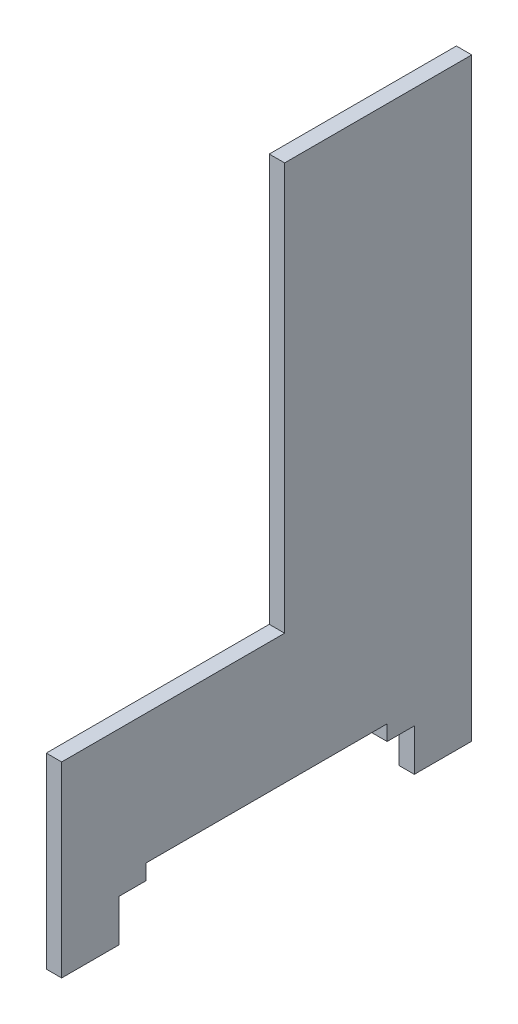
SolidWorks part; units mm, degrees
ref_plane "Front Plane" through (0, 0, 0) normal (0, 0, 1) x (1, 0, 0)
ref_plane "Top Plane" through (0, 0, 0) normal (0, 1, 0) x (1, 0, 0)
ref_plane "Right Plane" through (0, 0, 0) normal (1, 0, 0) x (0, 0, -1)
sketch "Sketch1" plane through (0, 0, 0) normal (0, 1, 0) x (1, 0, 0)
  line L0 (0, 0) -> (0, 40) construction
  line L1 (-40, 40) -> (40, 40) construction
  line L2 (-40, 40) -> (-40, -40) construction
  line L3 (-40, -40) -> (40, -40) construction
  line L4 (40, 40) -> (40, -40) construction
  line L5 (0, 0) -> (-40, 0) construction
  line L6 (-20, 60) -> (60, 60) construction
  line L7 (-37, -37) -> (37, -37) construction
  line L8 (37, 37) -> (37, -37) construction
  line L9 (-37, 37) -> (37, 37) construction
  line L10 (-37, 37) -> (-37, -37) construction
  line L11 (-37, -37) -> (-40, -37) construction
  line L12 (14.7, 20) -> (17.7, 20) construction
  line L13 (40, -31.8) -> (-40, -31.8) construction
  line L14 (-40, -28.8) -> (40, -28.8) construction
  line L15 (-40, -23.5) -> (40, -23.5) construction
  line L16 (0, -31.8) -> (0, -28.8) construction
  line L17 (0, -31.8) -> (0, -40) construction
  line L18 (0, -28.8) -> (0, -23.5) construction
  line L19 (43.5, 20) -> (48.8, 20) construction
  line L20 (51.8, 20) -> (60, 20) construction
  line L21 (40, 2.3) -> (-40, 2.3) construction
  line L22 (-40, 5.3) -> (40, 5.3) construction
  line L23 (3, 5.3) -> (3, 2.3) construction
  line L25 (40, -0.7) -> (-40, -0.7) construction
  line L26 (40, 8.3) -> (-40, 8.3) construction
  line L27 (3, 2.3) -> (3, -0.7) construction
  line L28 (3, 5.3) -> (3, 8.3) construction
  line L29 (17.7, 20) -> (20.7, 20) construction
  line L30 (19, 20) -> (56.5, 20) construction
  line L31 (3, 0) -> (0, 0) construction
  line L33 (40, 31.8) -> (-40, 31.8) construction
  line L34 (-40, 28.8) -> (40, 28.8) construction
  line L35 (-40, 23.5) -> (40, 23.5) construction
  line L36 (6, 2.3) -> (6, 1) construction
  line L37 (6, -36.5) -> (6, -40) construction
  line L38 (56.5, 20) -> (60, 20) construction
  line L40 (3, 0) -> (6, 0) construction
  line L41 (6, 1) -> (6, -36.5) construction
  line L42 (19, 20) -> (17.7, 20) construction
sketch "Sketch2" plane through (0, 0, 0) normal (1, 0, 0) x (0, 0, -1)
  line L0 (40, 0) -> (-40, 0) construction
  line L1 (40, 3.55) -> (-40, 3.55)
  line L2 (40, 3.55) -> (40, 119.507)
  line L3 (40, 119.507) -> (-40, 119.507) construction
  line L4 (-40, 3.55) -> (-40, 119.507) construction
  line L5 (40, -3.55) -> (-40, -3.55) construction
  line L6 (0, 0) -> (0, 119.507) construction
  line L7 (20, -5.5) -> (20, -47.5) construction
  line L8 (5.3, 47.5) -> (2.3, 47.5)
  line L9 (5.3, 47.5) -> (5.3, 5.5)
  line L10 (5.3, 5.5) -> (2.3, 5.5)
  line L11 (2.3, 47.5) -> (2.3, 5.5)
  line L12 (5.3, 5.5) -> (5.3, 3.55) construction
  line L13 (20, -5.5) -> (20, -3.55) construction
  line L14 (5.3, 26.5) -> (-36.5, 26.5) construction
  line L15 (20, -16.45) -> (20, -36.55) construction
  line L16 (-36.5, 36.55) -> (1, 36.55)
  line L17 (-36.5, 36.55) -> (-36.5, 16.45)
  line L18 (-36.5, 16.45) -> (1, 16.45)
  line L19 (1, 36.55) -> (1, 16.45)
  line L20 (37, 116.507) -> (37, 6.55) construction
  line L21 (37, 6.55) -> (-37, 6.55) construction
  line L22 (-37, 6.55) -> (-37, 116.507) construction
  line L23 (-37, 6.55) -> (-37, 3.55) construction
  line L24 (-37, 6.55) -> (-40, 6.55) construction
  line L25 (-23.5, 3.55) -> (-23.5, 6.55)
  line L26 (-23.5, 6.55) -> (-28.8, 6.55)
  line L27 (-28.8, 6.55) -> (-28.8, 11.75)
  line L28 (-28.8, 11.75) -> (-23.5, 11.75)
  line L29 (-23.5, 11.75) -> (-23.5, 14.75)
  line L30 (-23.5, 14.75) -> (-40, 14.75)
  line L31 (-31.8, 14.75) -> (-31.8, 3.55) construction
  line L32 (20, -6.55) -> (20, -11.75) construction
  line L33 (31.8, 14.75) -> (31.8, 3.55) construction
  line L34 (23.5, 14.75) -> (40, 14.75)
  line L35 (23.5, 11.75) -> (23.5, 14.75)
  line L36 (28.8, 11.75) -> (23.5, 11.75)
  line L37 (28.8, 6.55) -> (28.8, 11.75)
  line L38 (23.5, 6.55) -> (28.8, 6.55)
  line L39 (23.5, 3.55) -> (23.5, 6.55)
  line L40 (23.5, 14.75) -> (-23.5, 14.75) construction
  line L41 (37, 116.507) -> (-37, 116.507) construction
  line L43 (3.5, 119.507) -> (3.5, 40.05) construction
  line L44 (-37, 116.507) -> (-37, 119.507) construction
  line L45 (-37, 116.507) -> (-40, 116.507) construction
  line L46 (3.5, 40.05) -> (-40, 40.05)
  line L47 (6.5, 119.507) -> (6.5, 37.05) construction
  line L48 (6.5, 37.05) -> (-40, 37.05) construction
  line L49 (3.5, 40.05) -> (3.5, 37.05) construction
  line L50 (3.5, 40.05) -> (6.5, 40.05) construction
  line L51 (27.1, 60.207) -> (7, 60.207) construction
  line L52 (6.5, 37.05) -> (6.5, 3.55) construction
  line L53 (-36.5, 36.55) -> (-37, 36.55) construction
  line L54 (-36.5, 36.55) -> (-36.5, 37.05) construction
  line L55 (3.5, 37.05) -> (3.5, 3.55) construction
  line L56 (27.1, 60.207) -> (7, 60.207) construction
  line L57 (27.1, 60.207) -> (27.1, 114.507) construction
  line L58 (27.1, 114.507) -> (7, 114.507) construction
  line L59 (7, 60.207) -> (7, 114.507) construction
  line L60 (27.1, 114.507) -> (7, 114.507) construction
  line L61 (27.1, 107.857) -> (27.1, 66.857) construction
  line L62 (7, 107.857) -> (7, 66.857) construction
  line L63 (3.5, 98.4639) -> (6.5, 98.4639) construction
  line L64 (3.5, 55.3502) -> (6.5, 55.3502) construction
  circle A0 centre (17.05, 76.907) radius 21 construction
  circle A1 centre (17.05, 76.907) radius 21 construction
  circle A2 centre (17.05, 76.907) radius 24 construction
  dimension "D2" = 3
  dimension "D1" = 0.5
  dimension "D3" = 2
  dimension "D4" = 43.5
ref_plane "xslide" through (0, 26.5, 0) normal (0, 1, 0) x (1, 0, 0)
ref_plane "xgear" through (0, 0, -2.3) normal (0, 0, 1) x (1, 0, 0)
sketch "Sketch3" plane through (0, 0, 0) normal (0, 1, 0) x (1, 0, 0)
  line L0 (28.8, 31.8) -> (23.5, 31.8)
  line L1 (40, 40) -> (-40, 40)
  line L2 (40, 40) -> (40, -40)
  line L3 (40, -40) -> (-40, -40)
  line L4 (-40, 40) -> (-40, -40)
  line L5 (37, 37) -> (-37, 37) construction
  line L6 (37, 37) -> (37, -37) construction
  line L7 (37, -37) -> (-37, -37) construction
  line L8 (-37, 37) -> (-37, -37) construction
  line L9 (23.5, 31.8) -> (23.5, 28.8)
  line L10 (23.5, 28.8) -> (40, 28.8)
  line L11 (28.8, 31.8) -> (28.8, 37)
  line L12 (0, 0) -> (0, 40) construction
  line L13 (0, 0) -> (-40, 0) construction
  line L14 (-31.8, 28.8) -> (-31.8, 40)
  line L15 (-23.5, 28.8) -> (-40, 28.8)
  line L16 (-26.15, 31.8) -> (-26.15, 17.05) construction
  line L17 (31.8, 28.8) -> (31.8, 40)
  line L18 (-23.5, 31.8) -> (-23.5, 28.8)
  line L19 (28.8, 37) -> (23.5, 37)
  line L20 (23.5, 37) -> (23.5, 40)
  line L21 (28.8, 31.8) -> (31.8, 31.8) construction
  line L22 (31.8, 31.8) -> (40, 31.8) construction
  line L23 (37, 37) -> (40, 37) construction
  line L24 (48.8, 20) -> (54, 20) construction
  line L25 (51.8, 20) -> (60, 20) construction
  line L26 (48.8, 20) -> (43.5, 20) construction
  line L27 (-28.8, 31.8) -> (-23.5, 31.8)
  line L28 (-28.8, 31.8) -> (-28.8, 37)
  line L29 (-28.8, 37) -> (-23.5, 37)
  line L30 (-23.5, 37) -> (-23.5, 40)
  line L31 (23.5, 28.8) -> (-23.5, 28.8) construction
  line L32 (8.3, -6.95) -> (8.3, 41.05) construction
  line L33 (5.3, -3.95) -> (2.3, -3.95)
  line L34 (5.3, -3.95) -> (5.3, 38.05)
  line L35 (5.3, 38.05) -> (2.3, 38.05)
  line L36 (2.3, -3.95) -> (2.3, 38.05)
  line L37 (-26.15, 2.3) -> (-26.15, 0) construction
  line L38 (14.7, 20) -> (-27.3, 20) construction
  line L39 (-6.15, 20) -> (8.6, 20) construction
  line L40 (5.3, 17.05) -> (2.3, 17.05) construction
  line L41 (2.3, 17.05) -> (1, 17.05) construction
  line L42 (1, 17.05) -> (-36.5, 17.05) construction
  line L43 (19, 20) -> (17.7, 20) construction
  line L44 (19, 20) -> (56.5, 20) construction
  line L45 (56.5, 20) -> (76.6, 20) construction
  line L46 (-36.5, 7) -> (1, 7)
  line L47 (-36.5, 7) -> (-36.5, 27.1)
  line L48 (-36.5, 27.1) -> (1, 27.1)
  line L49 (1, 7) -> (1, 27.1)
  line L50 (8.3, 41.05) -> (-0.7, 41.05) construction
  line L51 (-0.7, -6.95) -> (-0.7, 41.05) construction
  line L52 (8.3, -6.95) -> (-0.7, -6.95) construction
  line L53 (5.3, 38.05) -> (8.3, 38.05) construction
  line L54 (14.7, 20) -> (11.7, 20) construction
  line L55 (40, 2.3) -> (-40, 2.3) construction
  line L57 (2.3, 38.05) -> (0, 38.05) construction
ref_plane "zgear" through (2.3, 0, 0) normal (1, 0, 0) x (0, 0, -1)
ref_plane "zslide" through (0, 0, -17.05) normal (0, 0, 1) x (1, 0, 0)
ref_plane "zstop" through (0, 14.75, 0) normal (0, 1, 0) x (1, 0, 0)
ref_plane "peak_left" through (-40, 0, 0) normal (1, 0, 0) x (0, 0, -1)
ref_plane "peak_right" through (40, 0, 0) normal (1, 0, 0) x (0, 0, -1)
ref_plane "peak_front" through (0, 0, -40) normal (0, 0, 1) x (1, 0, 0)
ref_plane "peak_back" through (0, 0, 40) normal (0, 0, 1) x (1, 0, 0)
ref_plane "peak_uno" through (0, 0, -3.5) normal (0, 0, 1) x (1, 0, 0)
ref_plane "peak_top" through (0, 119.507, 0) normal (0, 1, 0) x (1, 0, 0)
ref_plane "peak_bottom" through (0, 3.55, 0) normal (0, 1, 0) x (1, 0, 0)
sketch "Sketch4" plane through (-40, 0, 0) normal (1, 0, 0) x (0, 0, -1)
  line L0 (40, 119.507) -> (40, 3.55)
  line L1 (40, 3.55) -> (28.8, 3.55)
  line L2 (28.8, 3.55) -> (28.8, 11.75)
  line L3 (28.8, 11.75) -> (23.5, 11.75)
  line L4 (23.5, 11.75) -> (23.5, 14.75)
  line L5 (23.5, 14.75) -> (-23.5, 14.75)
  line L6 (-23.5, 14.75) -> (-23.5, 11.75)
  line L7 (-23.5, 11.75) -> (-28.8, 11.75)
  line L8 (-28.8, 11.75) -> (-28.8, 3.55)
  line L9 (-28.8, 3.55) -> (-40, 3.55)
  line L10 (-40, 3.55) -> (-40, 40.05)
  line L11 (-40, 40.05) -> (3.5, 40.05)
  line L12 (3.5, 40.05) -> (3.5, 119.507)
  line L13 (3.5, 119.507) -> (40, 119.507)
  line L14 (40, 119.507) -> (-40, 119.507) construction
  line L15 (40, 3.55) -> (-40, 3.55) construction
  line L16 (40, 3.55) -> (40, 119.507) construction
  line L17 (-40, 3.55) -> (-40, 119.507) construction
  line L18 (3.5, 40.05) -> (-40, 40.05) construction
  line L19 (3.5, 119.507) -> (3.5, 40.05) construction
  line L20 (23.5, 14.75) -> (-23.5, 14.75) construction
  line L21 (23.5, 11.75) -> (23.5, 14.75) construction
  line L22 (-23.5, 11.75) -> (-23.5, 14.75) construction
  line L23 (-28.8, 6.55) -> (-28.8, 11.75) construction
  line L24 (28.8, 6.55) -> (28.8, 11.75) construction
  line L25 (28.8, 11.75) -> (23.5, 11.75) construction
  line L26 (-28.8, 11.75) -> (-23.5, 11.75) construction
sketch "Sketch5" plane through (0, 0, -40) normal (0, 0, 1) x (1, 0, 0)
  line L1 (-40, 119.507) -> (-37, 119.507)
  line L2 (-40, 119.507) -> (-40, 3.55)
  line L3 (-40, 3.55) -> (-37, 3.55)
  line L4 (-37, 119.507) -> (-37, 3.55)
extrude "Boss-Extrude1" add sketch "Sketch4" along normal up to vertex (3 mm away) up to point (-37, 3.55, -40)
